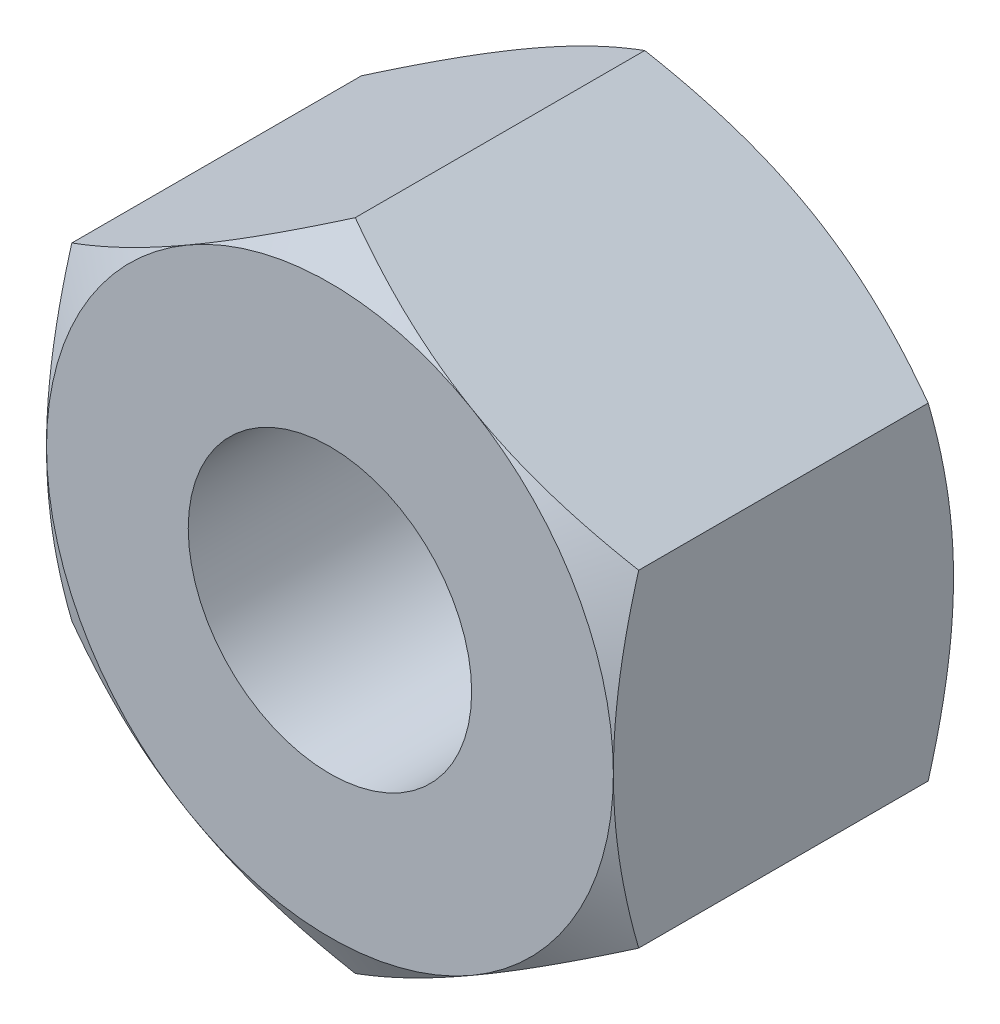
SolidWorks part; units mm, degrees
ref_plane "Plan de face" through (0, 0, 0) normal (0, 0, 1) x (1, 0, 0)
ref_plane "Plan de dessus" through (0, 0, 0) normal (0, 1, 0) x (1, 0, 0)
ref_plane "Plan de droite" through (0, 0, 0) normal (1, 0, 0) x (0, 0, -1)
sketch "Esquisse1" plane through (0, 0, 0) normal (0, 0, 1) x (1, 0, 0)
  line L1 (0, 5.7735) -> (-5, 2.8868)
  line L2 (-5, 2.8868) -> (-5, -2.8868)
  line L3 (-5, -2.8868) -> (0, -5.7735)
  line L4 (0, -5.7735) -> (5, -2.8868)
  line L5 (5, -2.8868) -> (5, 2.8868)
  line L6 (5, 2.8868) -> (0, 5.7735)
  circle A0 centre (0, 0) radius 5 construction
  dimension "D1" = 10
extrude "Boss.-Extru.1" add sketch "Esquisse1" along normal blind 6
sketch "Esquisse2" plane through (0, 0, 6) normal (0, 0, 1) x (1, 0, 0)
  circle A0 centre (0, 0) radius 2.5
  dimension "D1" = 5
extrude "Enlèv. mat.-Extru.1" cut sketch "Esquisse2" against normal up to next
sketch "Esquisse4" plane through (0, 0, 0) normal (0, 1, 0) x (1, 0, 0)
  line L0 (-10.1962, -3) -> (-3.2679, 1)
  line L1 (0, 0) -> (-5, 0) construction
  line L3 (-10.1962, -3) -> (-3.2679, -7)
  line L4 (-3.2679, 1) -> (-11.1962, 1)
  line L5 (-11.1962, 1) -> (-11.1962, -7)
  line L6 (-11.1962, -7) -> (-3.2679, -7)
  line L7 (0, 0) -> (0, -6) construction
  dimension "D1" = 1
  dimension "D2" = 1
  dimension "D3" = 30
revolve "Enlèvement de matière-Révolution8" cut sketch "Esquisse4" angle 360 about L7
